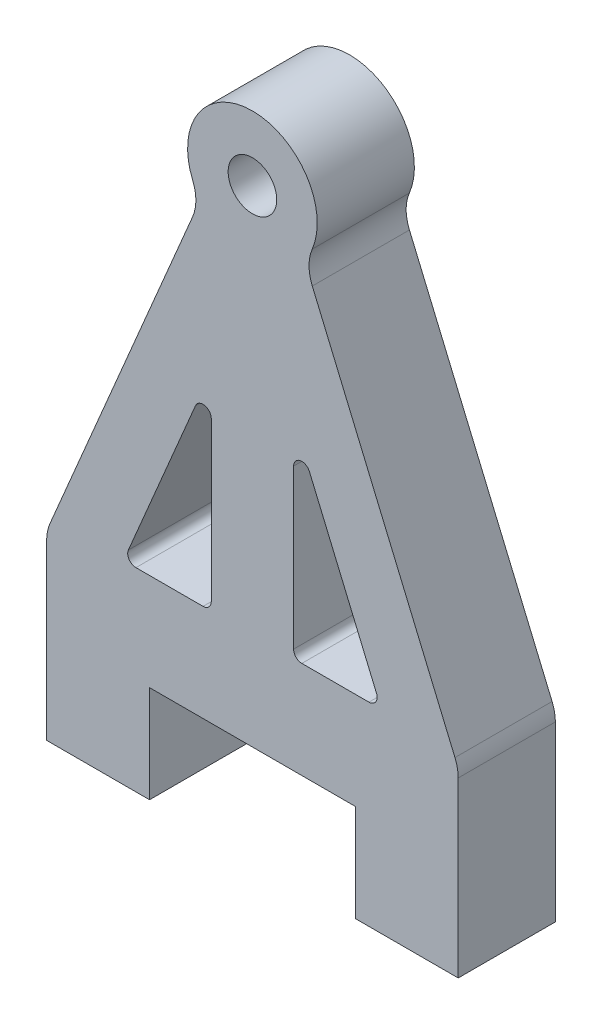
SolidWorks part; units mm, degrees
ref_plane "Front Plane" through (0, 0, 0) normal (0, 0, 1) x (1, 0, 0)
ref_plane "Top Plane" through (0, 0, 0) normal (0, 1, 0) x (1, 0, 0)
ref_plane "Right Plane" through (0, 0, 0) normal (1, 0, 0) x (0, 0, -1)
sketch "Sketch1" plane through (0, 0, 0) normal (0, 0, 1) x (1, 0, 0)
  line L0 (-3.048, -24.0056) -> (-7.1891, -24.0056)
  line L1 (-2.54, -13.7155) -> (-2.54, -23.4976)
  line L2 (-12.7, -30) -> (-12.7, -35.9944)
  line L3 (-6.35, -30) -> (6.35, -30)
  line L4 (12.7, -30) -> (12.7, -25.3031)
  line L5 (-12.7, -35.9944) -> (-6.35, -35.9944)
  line L6 (-12.7, -25.3031) -> (-12.7, -30)
  line L7 (7.1891, -24.0056) -> (3.048, -24.0056)
  line L8 (-6.35, -35.9944) -> (-6.35, -30)
  line L9 (12.7, -30) -> (12.7, -35.9944)
  line L10 (12.7, -35.9944) -> (6.35, -35.9944)
  line L11 (3.5158, -13.5175) -> (7.6569, -23.2996)
  line L12 (-3.5158, -13.5175) -> (-7.6569, -23.2996)
  line L13 (3.6943, -3.5142) -> (12.499, -24.3129)
  line L14 (6.35, -35.9944) -> (6.35, -30)
  line L15 (-3.6943, -3.5142) -> (-12.499, -24.3129)
  line L24 (2.54, -13.7155) -> (2.54, -23.4976)
  circle A0 centre (0, 0) radius 1.5
  arc A1 (3.6901, -1.5438) -> (-3.6901, -1.5438) centre (0, 0) ccw
  arc A2 (-3.6943, -3.5142) -> (-3.6901, -1.5438) centre (-6.0333, -2.524) ccw
  arc A3 (3.6943, -3.5142) -> (3.6901, -1.5438) centre (6.0333, -2.524) cw
  arc A4 (-2.54, -13.7155) -> (-3.5158, -13.5175) centre (-3.048, -13.7155) ccw
  arc A5 (2.54, -13.7155) -> (3.5158, -13.5175) centre (3.048, -13.7155) cw
  arc A6 (-7.6569, -23.2996) -> (-7.1891, -24.0056) centre (-7.1891, -23.4976) ccw
  arc A7 (7.6569, -23.2996) -> (7.1891, -24.0056) centre (7.1891, -23.4976) cw
  arc A8 (2.54, -23.4976) -> (3.048, -24.0056) centre (3.048, -23.4976) ccw
  arc A9 (-3.048, -24.0056) -> (-2.54, -23.4976) centre (-3.048, -23.4976) ccw
  arc A10 (-12.499, -24.3129) -> (-12.7, -25.3031) centre (-10.16, -25.3031) ccw
  arc A11 (12.499, -24.3129) -> (12.7, -25.3031) centre (10.16, -25.3031) cw
  point P12 (0, -30)
  dimension "D1" = 2.54
  dimension "D2" = 2.54
  dimension "D3" = 0.508
  dimension "D4" = 0.508
  dimension "D5" = 0.508
  dimension "D6" = 0.508
  dimension "D7" = 0.508
  dimension "D8" = 0.508
  dimension "D9" = 2.54
  dimension "D10" = 2.54
extrude "Boss-Extrude1" add sketch "Sketch1" along normal blind 5.9944 contours L15 A10 L6 L3 L4 A11 L13 A3 A1 A2
